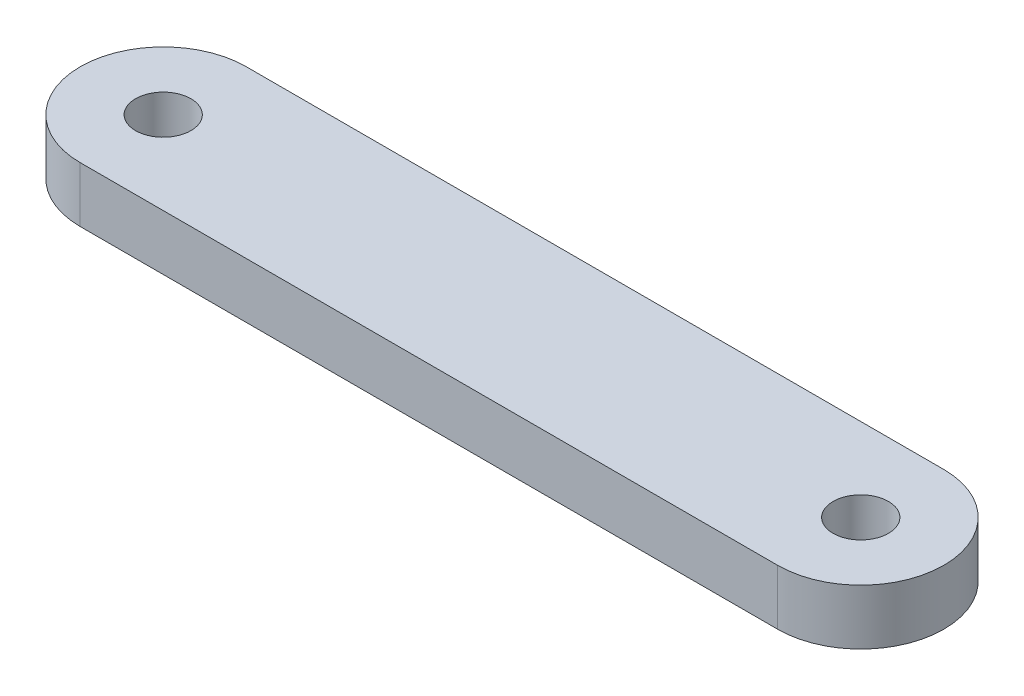
SolidWorks part; units mm, degrees
ref_plane "Alzado" through (0, 0, 0) normal (0, 0, 1) x (1, 0, 0)
ref_plane "Planta" through (0, 0, 0) normal (0, 1, 0) x (1, 0, 0)
ref_plane "Vista lateral" through (0, 0, 0) normal (1, 0, 0) x (0, 0, -1)
sketch "Croquis1" plane through (0, 0, 0) normal (0, 1, 0) x (1, 0, 0)
  line L1 (-20, 0) -> (20, 0)
  line L3 (-20, -9.525) -> (20, -9.525)
  arc A0 (-20, 0) -> (-20, -9.525) centre (-20, -4.7625) ccw
  arc A1 (20, -9.525) -> (20, 0) centre (20, -4.7625) ccw
  circle A2 centre (-20, -4.7625) radius 1.5875
  circle A3 centre (20, -4.7625) radius 1.5875
  dimension "D3" = 4.7625
  dimension "D5" = 3.175
  dimension "D6" = 3.175
  dimension "D1" = 40
  dimension "D2" = 9.525
  dimension "D4" = 40
extrude "Saliente-Extruir1" add sketch "Croquis1" along normal blind 3.175
